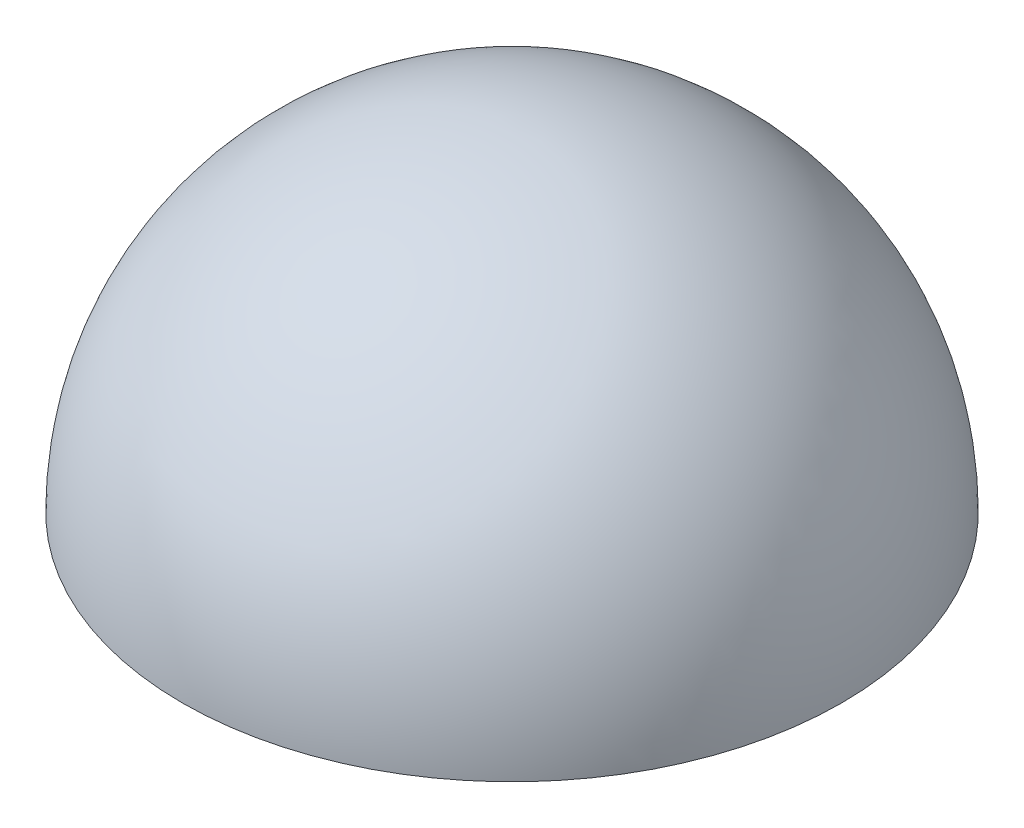
SolidWorks part; units mm, degrees
ref_plane "Front Plane" through (0, 0, 0) normal (0, 0, 1) x (1, 0, 0)
ref_plane "Top Plane" through (0, 0, 0) normal (0, 1, 0) x (1, 0, 0)
ref_plane "Right Plane" through (0, 0, 0) normal (1, 0, 0) x (0, 0, -1)
sketch "Esquisse1" plane through (0, 0, 0) normal (0, 0, 1) x (1, 0, 0)
  line L0 (0, 0) -> (0, 185.8945) construction
  line L1 (0, 72) -> (0, 77)
  line L2 (77, 0) -> (72, 0)
  arc A0 (72, 0) -> (0, 72) centre (0, 0) ccw
  arc A1 (77, 0) -> (0, 77) centre (0, 0) ccw
  dimension "D1" = 72
  dimension "D2" = 5
  dimension "D3" = 5
revolve "Révolution1" add sketch "Esquisse1" angle 360 about L0
